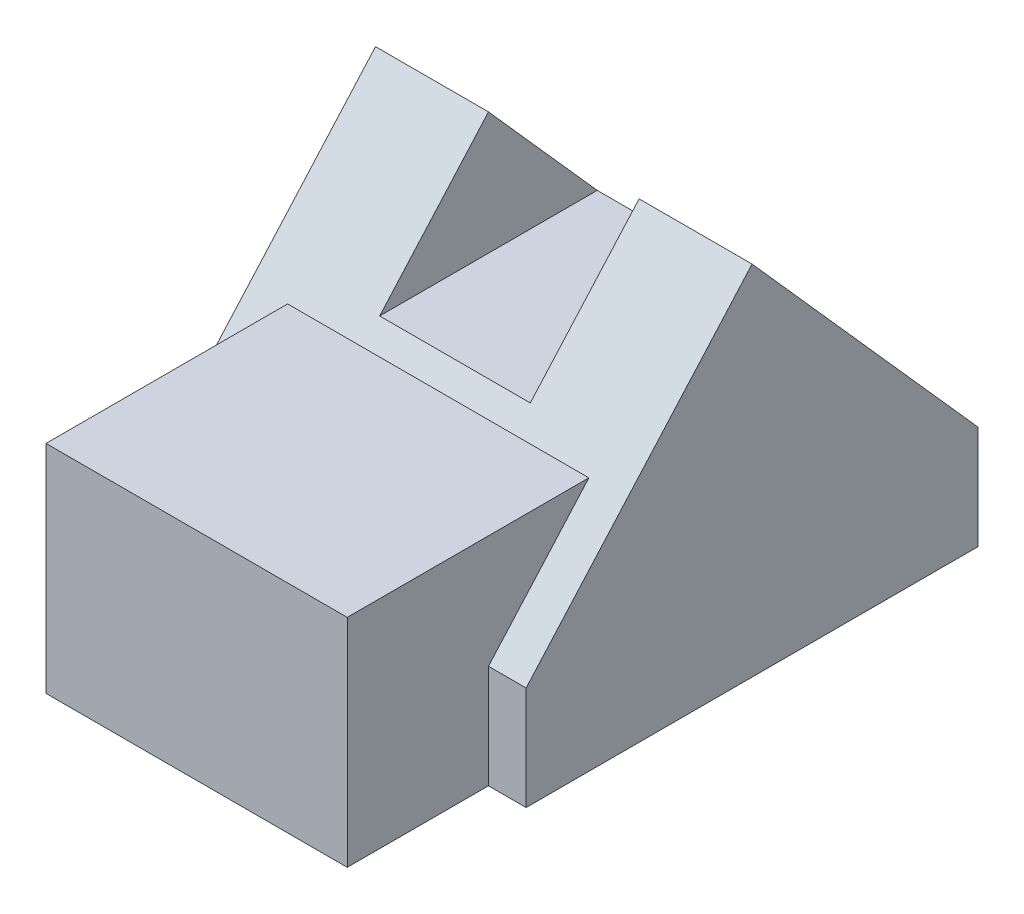
SolidWorks part; units mm, degrees
material "AISI 1020"
ref_plane "Alzado" through (0, 0, 0) normal (0, 0, 1) x (1, 0, 0)
ref_plane "Planta" through (0, 0, 0) normal (0, 1, 0) x (1, 0, 0)
ref_plane "Vista lateral" through (0, 0, 0) normal (1, 0, 0) x (0, 0, -1)
sketch "Croquis1" plane through (0, 0, 0) normal (0, 1, 0) x (1, 0, 0)
  line L1 (0, 0) -> (40, 0)
  line L2 (0, 0) -> (0, 63)
  line L3 (0, 63) -> (40, 63)
  line L4 (40, 0) -> (40, 63)
  dimension "D1" = 63
  dimension "D2" = 40
extrude "Saliente-Extruir1" add sketch "Croquis1" along normal blind 38
sketch "Croquis2" plane through (0, 38, 0) normal (0, 1, 0) x (1, 0, 0)
  line L0 (0, 0) -> (4, 0)
  line L1 (0, 0) -> (40, 0) construction
  line L2 (0, 0) -> (0, 15)
  line L3 (0, 63) -> (0, 0) construction
  line L4 (0, 15) -> (4, 15)
  line L5 (4, 15) -> (4, 0)
  line L7 (40, 15) -> (36, 15)
  line L8 (40, 0) -> (40, 15)
  line L9 (40, 0) -> (36, 0)
  line L10 (36, 15) -> (36, 0)
extrude "Cortar-Extruir1" cut sketch "Croquis2" against normal blind 38
sketch "Croquis5" plane through (40, 0, 0) normal (1, 0, 0) x (0, 0, -1)
  line L0 (15, 0) -> (15, 11)
  line L1 (15, 0) -> (15, 38) construction
  line L2 (63, 0) -> (63, 11)
  line L3 (63, 38) -> (63, 0) construction
  line L4 (15, 11) -> (39, 38)
  line L5 (15, 38) -> (63, 38) construction
  line L6 (39, 38) -> (63, 11)
  line L7 (15, 11) -> (15, 38)
  line L8 (15, 38) -> (39, 38)
  line L9 (63, 38) -> (63, 11)
  line M4 (63, 38) -> (15, 38)
  line M5 (15, 38) -> (15, 0)
  line M7 (63, 0) -> (63, 38)
extrude "Cortar-Extruir2" cut sketch "Croquis5" against normal blind 4 contours L4 M5 M4 | L6 M4 M7
sketch "Croquis11" plane through (40, 0, 0) normal (1, 0, 0) x (0, 0, -1)
  line L4 (52.3333, 23) -> (39, 38)
  line L5 (39, 38) -> (52.3333, 38)
  line L10 (15, 11) -> (39, 38) construction
  line L12 (39, 38) -> (63, 11) construction
  line L13 (25.6667, 23) -> (25.6667, 37.9427)
  line L14 (25.6667, 37.9427) -> (39, 38)
  line L15 (39, 38) -> (25.6667, 23)
  line L16 (52.3333, 38) -> (52.3333, 23)
  line L18 (52.3333, 23) -> (39, 38)
  line M10 (63, 11) -> (39, 38)
extrude "Cortar-Extruir14" cut sketch "Croquis11" against normal blind 60 contours L16 L5 M10
sketch "Croquis19" plane through (40, 0, 0) normal (1, 0, 0) x (0, 0, -1)
  line L2 (15, 11) -> (39, 38) construction
  line L3 (25.6667, 23) -> (39, 38)
  line L4 (39, 38) -> (63, 11) construction
  line L5 (39, 38) -> (25.6667, 38)
  line L6 (25.6667, 38) -> (25.6667, 23)
extrude "Cortar-Extruir15" cut sketch "Croquis19" against normal blind 40 contours L3 L5 L6
sketch "Croquis20" plane through (40, 0, 0) normal (1, 0, 0) x (0, 0, -1)
  line L1 (25.6667, 23) -> (0, 23)
  line L2 (25.6667, 23) -> (25.6667, 38)
  line L3 (25.6667, 38) -> (0, 38)
  line L4 (0, 23) -> (0, 38)
  line L5 (52.3333, 23) -> (63, 23)
  line L6 (52.3333, 23) -> (52.3333, 38)
  line L7 (52.3333, 38) -> (63, 38)
  line L8 (63, 23) -> (63, 38)
extrude "Cortar-Extruir16" cut sketch "Croquis20" against normal blind 40
sketch "Croquis22" plane through (0, 0, 0) normal (0, 0, 1) x (1, 0, 0)
  line L1 (0, 38) -> (40, 38) construction
  line L2 (12, 38) -> (28, 38)
  line L7 (12, 38) -> (12, 25)
  line L8 (12, 25) -> (28, 25)
  line L9 (28, 25) -> (28, 38)
extrude "Cortar-Extruir17" cut sketch "Croquis22" against normal blind 72
sketch "Croquis23" plane through (0, 0, 0) normal (-1, 0, 0) x (0, 0, 1)
  line L0 (-15, 11) -> (-15, 23)
  line L1 (-63, 23) -> (-63, 0) construction
  line L2 (-15, 0) -> (-15, 11)
  line L3 (-15, 0) -> (-15, 23) construction
  line L4 (-63, 11) -> (-52.3333, 23)
  line L5 (-52.3333, 23) -> (-63, 23)
  line L6 (-63, 23) -> (-63, 11)
  line L7 (-15, 23) -> (-25.6667, 23)
  line L8 (-25.6667, 23) -> (-15, 11)
  line M9 (-15, 0) -> (-15, 23)
  line M10 (-15, 23) -> (-25.6667, 23)
  line M13 (-52.3333, 23) -> (-63, 23)
  line M14 (-63, 23) -> (-63, 0)
extrude "Cortar-Extruir19" cut sketch "Croquis23" against normal blind 40 contours L4 M14 M13 | L8 M10 M9
sketch "Croquis24" plane through (0, 0, 0) normal (-1, 0, 0) x (0, 0, 1)
  line L0 (-15, 11) -> (-15, 23)
  line L1 (-15, 23) -> (-25.6667, 23)
  line L2 (-15, 11) -> (-39, 38) construction
  line L3 (-25.6667, 23) -> (-15, 11)
extrude "Saliente-Extruir2" add sketch "Croquis24" against normal blind 36
sketch "Croquis26" plane through (0, 0, 0) normal (-1, 0, 0) x (0, 0, 1)
  line L0 (-15, 23) -> (-25.6667, 23)
  line L1 (-15, 23) -> (-15, 11)
  line L2 (-15, 0) -> (-15, 23) construction
  line L3 (-15, 11) -> (-25.6667, 23)
extrude "Cortar-Extruir20" cut sketch "Croquis26" against normal blind 4 contours L3 L0 L1
